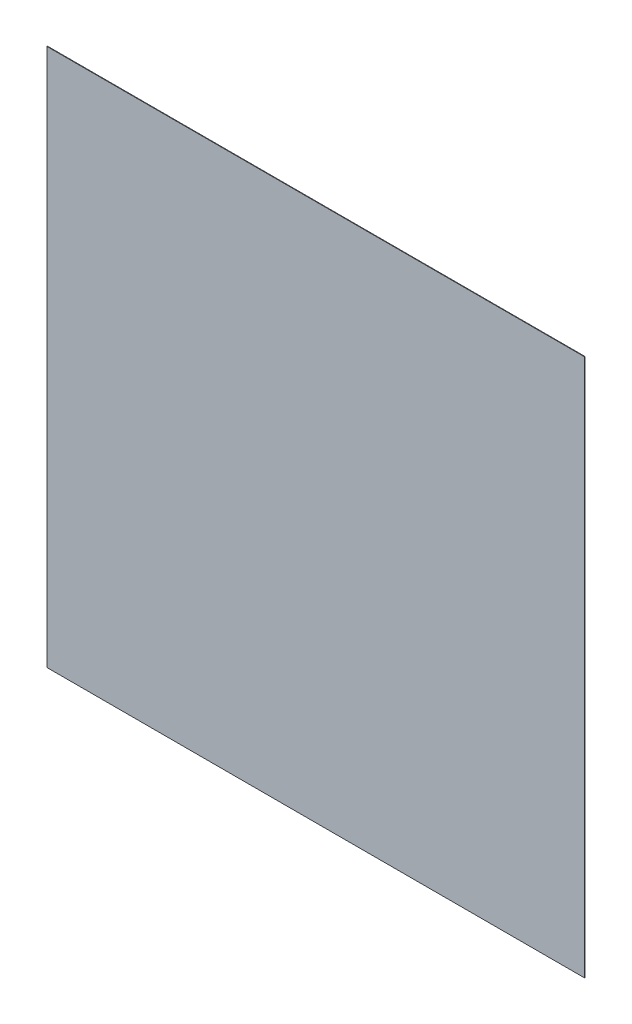
SolidWorks part; units mm, degrees
ref_plane "Plan de face" through (0, 0, 0) normal (0, 0, 1) x (1, 0, 0)
ref_plane "Plan de dessus" through (0, 0, 0) normal (0, 1, 0) x (1, 0, 0)
ref_plane "Plan de droite" through (0, 0, 0) normal (1, 0, 0) x (0, 0, -1)
sketch "Esquisse1" plane through (0, 0, 0) normal (0, 0, 1) x (1, 0, 0)
  line L1 (-5000, -5000) -> (5000, -5000)
  line L2 (-5000, -5000) -> (-5000, 5000)
  line L3 (-5000, 5000) -> (5000, 5000)
  line L4 (5000, -5000) -> (5000, 5000)
  line L5 (-5000, -5000) -> (5000, 5000) construction
  line L6 (-5000, 5000) -> (5000, -5000) construction
  point P0 (0, 0)
  dimension "D1" = 10000
  dimension "D2" = 10000
extrude "Boss.-Extru.1" add sketch "Esquisse1" along normal blind 10
